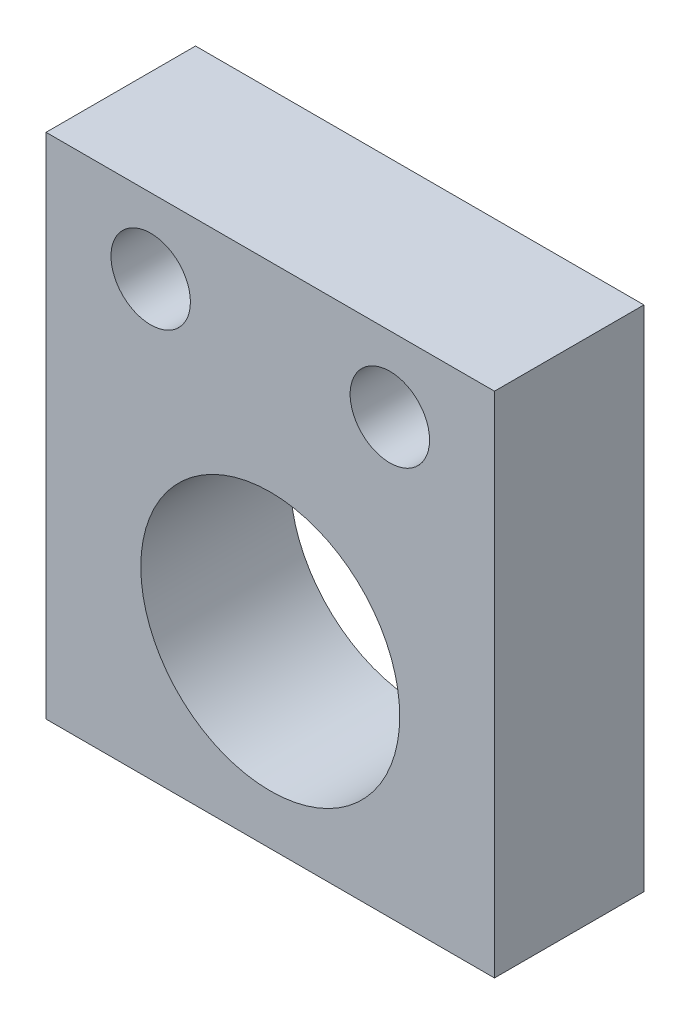
SolidWorks part; units mm, degrees
material "6063-T5"
ref_plane "Front Plane" through (0, 0, 0) normal (0, 0, 1) x (1, 0, 0)
ref_plane "Top Plane" through (0, 0, 0) normal (0, 1, 0) x (1, 0, 0)
ref_plane "Right Plane" through (0, 0, 0) normal (1, 0, 0) x (0, 0, -1)
sketch "Sketch1" plane through (0, 0, 0) normal (0, 0, 1) x (1, 0, 0)
  line L1 (0, 0) -> (38.1, 0)
  line L2 (0, 0) -> (0, 43.18)
  line L3 (0, 43.18) -> (38.1, 43.18)
  line L4 (38.1, 0) -> (38.1, 43.18)
  dimension "D1" = 38.1
  dimension "D2" = 43.18
extrude "Boss-Extrude1" add sketch "Sketch1" against normal blind 12.7
sketch "Sketch3" plane through (0, 0, 0) normal (0, 0, 1) x (1, 0, 0)
  line L0 (19.05, -987.2485) -> (19.05, 49012.7515) construction
  line L1 (0, 43.18) -> (0, 0) construction
  line L2 (38.1, 0) -> (38.1, 43.18) construction
  line L3 (38.1, 43.18) -> (0, 43.18) construction
  circle A0 centre (19.05, 15.24) radius 11
  point P8 (0, 0)
  point P12 (0, 0)
  dimension "D1" = 27.94
extrude "Cut-Extrude1" cut sketch "Sketch3" against normal through all contours A0
sketch "Sketch5" plane through (0, 0, 0) normal (0, 0, 1) x (1, 0, 0)
  line L0 (19.05, -968.1712) -> (19.05, 49031.8288) construction
  line L1 (0, 43.18) -> (0, 0) construction
  line L2 (38.1, 0) -> (38.1, 43.18) construction
  line L3 (38.1, 43.18) -> (0, 43.18) construction
  point P6 (8.89, 36.83)
  point P7 (29.21, 36.83)
  dimension "D1" = 20.32
  dimension "D2" = 6.35
hole_wizard "17/64 (0.26563) Diameter Hole1" positions "3DSketch2" profile "Sketch7" hole size "17/64" standard "ANSI Inch" end condition through all
sketch3d "3DSketch2"
  point P0 (29.21, 36.83, 0)
  point P3 (8.89, 36.83, 0)
sketch "Sketch7" plane through (29.21, 36.83, 0) normal (1, 0, 0) x (0, -1, 0)
  line L0 (0, 0) -> (0, 12.7)
  line L1 (0, 12.7) -> (3.3735, 12.7)
  line L2 (3.3735, 12.7) -> (3.3735, 0)
  line L5 (3.3735, 0) -> (0, 0)
  line L11 (0, -6.35) -> (0, 107.95) construction
  dimension "Thru Hole Dia." = 6.747
  dimension "Thru Hole Depth" = 12.7
